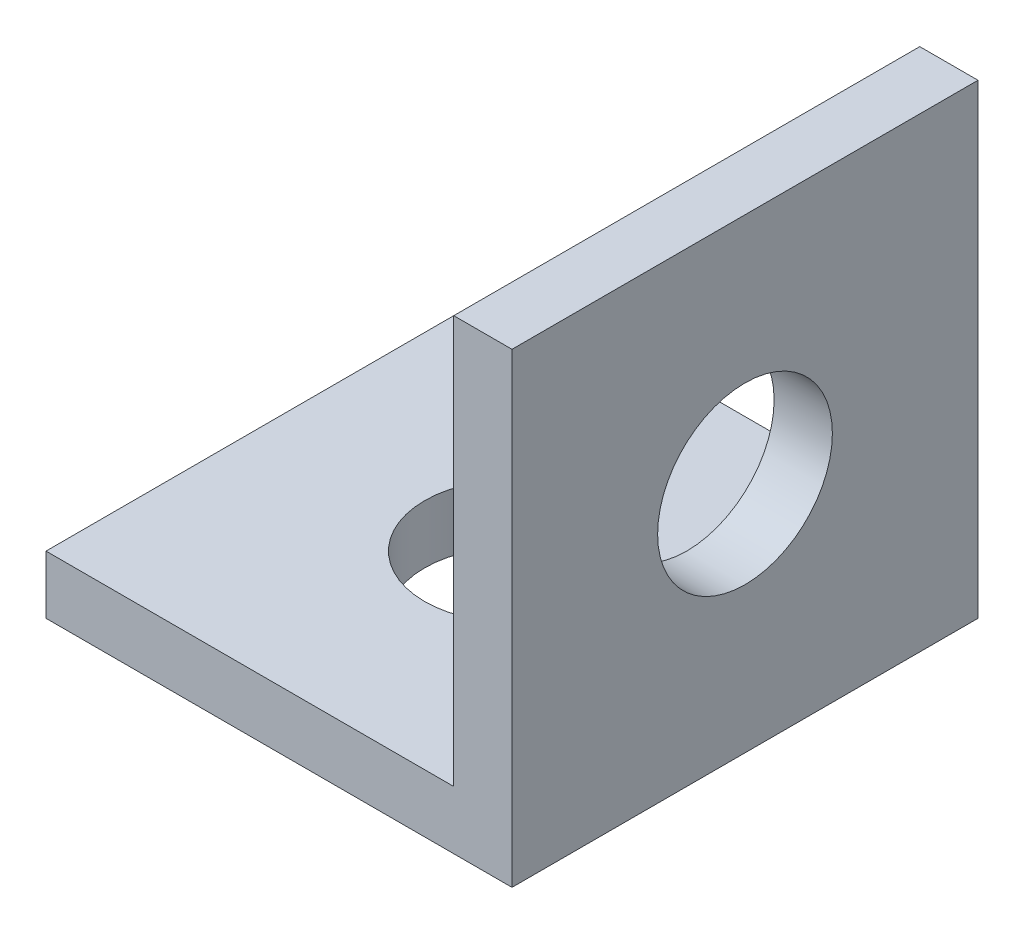
SolidWorks part; units mm, degrees
ref_plane "Face" through (0, 0, 0) normal (0, 0, 1) x (1, 0, 0)
ref_plane "Dessus" through (0, 0, 0) normal (0, 1, 0) x (1, 0, 0)
ref_plane "Droite" through (0, 0, 0) normal (1, 0, 0) x (0, 0, -1)
sketch "Esquisse1" plane through (0, 0, 0) normal (0, 1, 0) x (1, 0, 0)
  line L0 (4, 8) -> (4, 0) construction
  line L1 (0, 0) -> (8, 0)
  line L2 (0, 0) -> (0, 8)
  line L3 (0, 8) -> (8, 8)
  line L4 (8, 0) -> (8, 8)
  line L5 (0, 4) -> (8, 4) construction
  circle A0 centre (4, 4) radius 1.5
  dimension "D3" = 3
  dimension "D1" = 8
  dimension "D2" = 8
extrude "Extrusion1" add sketch "Esquisse1" along normal blind 1
sketch "Esquisse2" plane through (0, 1, 0) normal (0, 1, 0) x (1, 0, 0)
  line L0 (8, 8) -> (0, 8) construction
  line L1 (8, 0) -> (7, 0)
  line L2 (8, 0) -> (8, 8)
  line L3 (8, 8) -> (7, 8)
  line L4 (7, 0) -> (7, 8)
  dimension "D1" = 1
extrude "Extrusion2" add sketch "Esquisse2" along normal blind 7
sketch "Esquisse3" plane through (8, 0, 0) normal (1, 0, 0) x (0, 0, -1)
  line L0 (4, 8) -> (4, 0) construction
  line L1 (0, 8) -> (8, 8) construction
  line L2 (0, 0) -> (8, 0) construction
  line L3 (8, 4) -> (0, 4) construction
  line L4 (8, 8) -> (8, 0) construction
  line L5 (0, 8) -> (0, 0) construction
  circle A0 centre (4, 4) radius 1.5
  dimension "D1" = 3
extrude "Extrusion3" cut sketch "Esquisse3" against normal up to next
